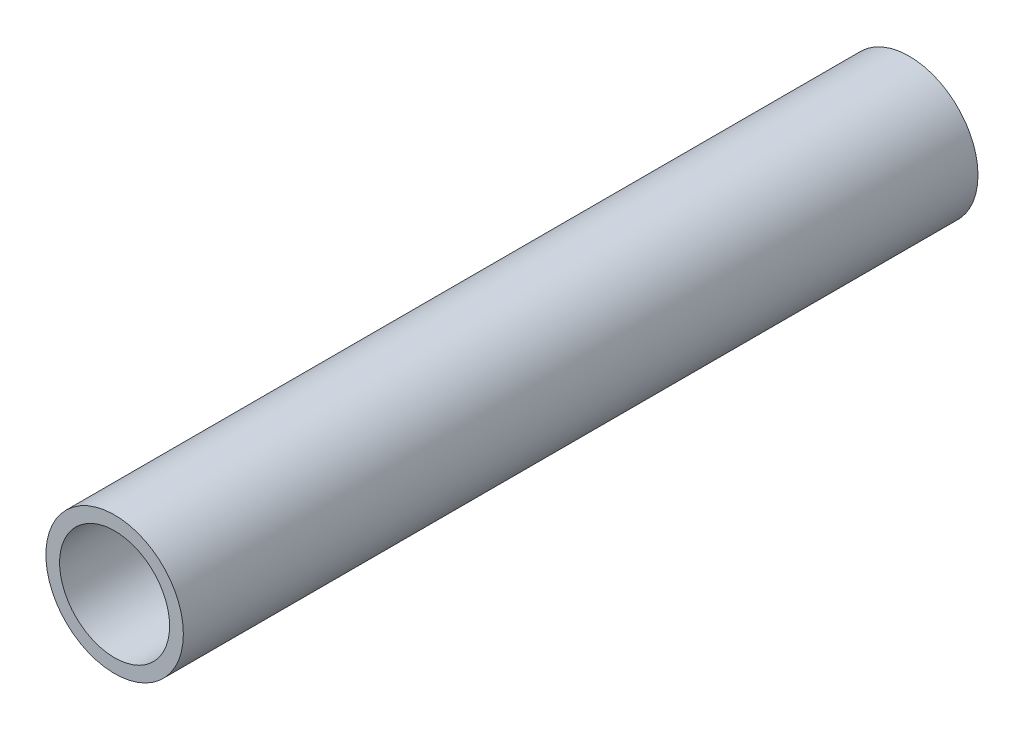
SolidWorks part; units mm, degrees
ref_plane "Front Plane" through (0, 0, 0) normal (0, 0, 1) x (1, 0, 0)
ref_plane "Top Plane" through (0, 0, 0) normal (0, 1, 0) x (1, 0, 0)
ref_plane "Right Plane" through (0, 0, 0) normal (1, 0, 0) x (0, 0, -1)
sketch "Sketch1" plane through (0, 0, 0) normal (0, 0, 1) x (1, 0, 0)
  circle A0 centre (0, 0) radius 1.25
  circle A1 centre (0, 0) radius 1
extrude "Boss-Extrude1" add sketch "Sketch1" along normal blind 14.45
